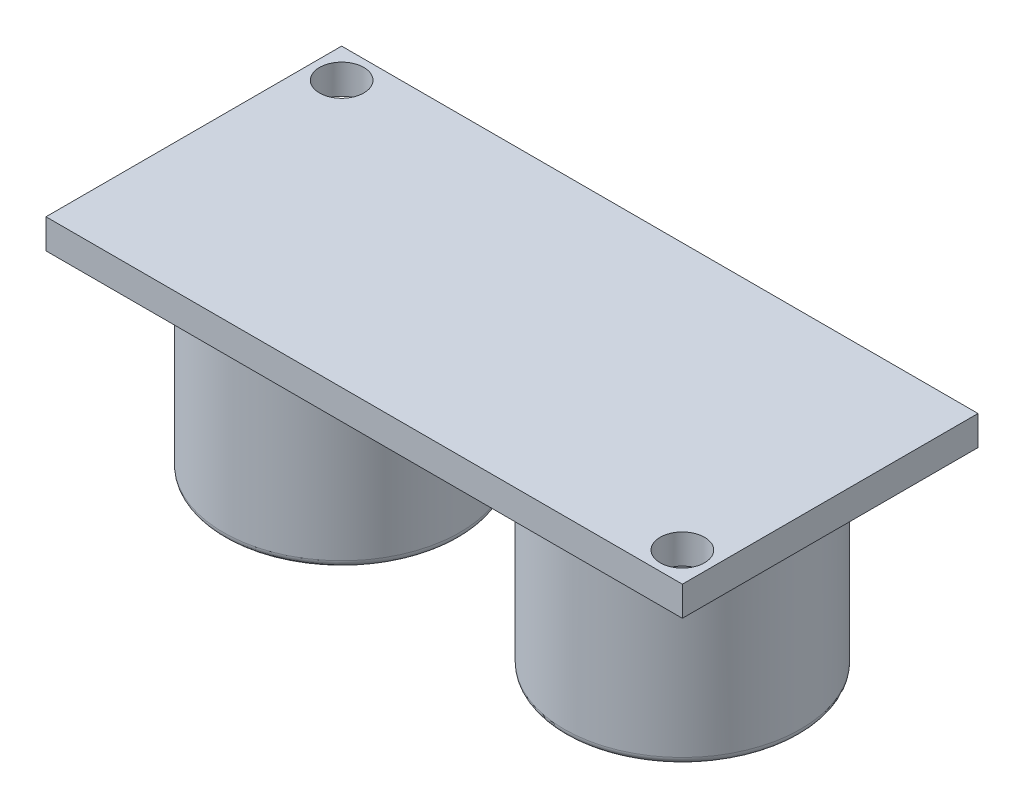
SolidWorks part; units mm, degrees
material "Elaborazione scheda, Semplice"
ref_plane "Piano frontale" through (0, 0, 0) normal (0, 0, 1) x (1, 0, 0)
ref_plane "Piano superiore" through (0, 0, 0) normal (0, 1, 0) x (1, 0, 0)
ref_plane "Piano destro" through (0, 0, 0) normal (1, 0, 0) x (0, 0, -1)
ref_plane "Piano1" through (0, -1, 0) normal (0, -1, 0) x (1, 0, 0)
sketch "Schizzo1" plane through (0, -1, 0) normal (0, -1, 0) x (1, 0, 0)
  line L0 (-21.525, 10) -> (-21.525, -10)
  line L1 (-21.525, -10) -> (21.525, -10)
  line L2 (21.525, -10) -> (21.525, 10)
  line L3 (21.525, 10) -> (-21.525, 10)
  dimension "D1" = 43.05
  dimension "D2" = 20
extrude "Estrusione-Estrusione1" add sketch "Schizzo1" against normal blind 2
sketch "Schizzo2" plane through (0, -1, 0) normal (0, -1, 0) x (1, 0, 0)
  line L0 (-1.7765, -8.759) -> (-1.7765, -5.241)
  line L1 (1.7941, -5.259) -> (1.7941, -8.741)
  line L2 (-21.525, 10) -> (-21.525, -10) construction
  line L3 (21.525, 10) -> (-21.525, 10) construction
  arc A0 (-1.7765, -5.241) -> (1.7941, -5.259) centre (0, -7) cw
  arc A1 (1.7941, -8.741) -> (-1.7765, -8.759) centre (0, -7) cw
  dimension "D1" = 2.5
  dimension "D2" = 2.5
  dimension "D3" = 19.7485
  dimension "D4" = 21.525
  dimension "D5" = 23.3191
  dimension "D6" = 15.241
extrude "Estrusione-Estrusione2" add sketch "Schizzo2" along normal blind 2.5
ref_plane "Piano2" through (0, 0, 0) normal (0, 0, -1) x (-1, 0, 0)
sketch "Schizzo3" plane through (0, 0, 0) normal (0, 0, -1) x (-1, 0, 0)
  line L0 (3.525, -14) -> (11.525, -14)
  line L1 (11.525, -14) -> (11.525, -1)
  line L2 (11.525, -1) -> (3.525, -1)
  line L3 (3.525, -1) -> (3.525, -14)
  line L4 (11.525, -14) -> (11.525, -1) construction
  dimension "D1" = 8
  dimension "D2" = 13
revolve "Rivoluzione1" add sketch "Schizzo3" angle 360 about L4
sketch "Schizzo4" plane through (0, 0, 0) normal (0, 0, -1) x (-1, 0, 0)
  line L0 (-19.525, -14) -> (-11.525, -14)
  line L1 (-11.525, -14) -> (-11.525, -1)
  line L2 (-11.525, -1) -> (-19.525, -1)
  line L3 (-19.525, -1) -> (-19.525, -14)
  line L4 (-11.525, -14) -> (-11.525, -1) construction
  dimension "D1" = 8
  dimension "D2" = 13
revolve "Rivoluzione2" add sketch "Schizzo4" angle 360 about L4
hole_wizard "Foro Ø3.0 (3)-1" positions "Schizzo6" profile "Schizzo5" hole size "Ø3.0" standard "Ansi Metric"
sketch "Schizzo6" plane through (0, 1, 0) normal (0, 1, 0) x (1, 0, 0)
  point P0 (-19.525, 8)
  point P1 (19.525, -8)
sketch "Schizzo5" plane through (-19.525, 1, -8) normal (1, 0, 0) x (0, 0, 1)
  line L0 (0, 0) -> (0, 15)
  line L1 (0, 15) -> (1.5, 15)
  line L2 (1.5, 15) -> (1.5, 0)
  line L5 (1.5, 0) -> (0, 0)
  line L11 (0, -6.35) -> (0, 107.95) construction
  dimension "Thru Hole Dia." = 3
  dimension "Thru Hole Depth" = 15
fillet "Raccordo1" radius 0.5 2 edges at (3.525, -14, 0) (-11.525, -14, 8)
